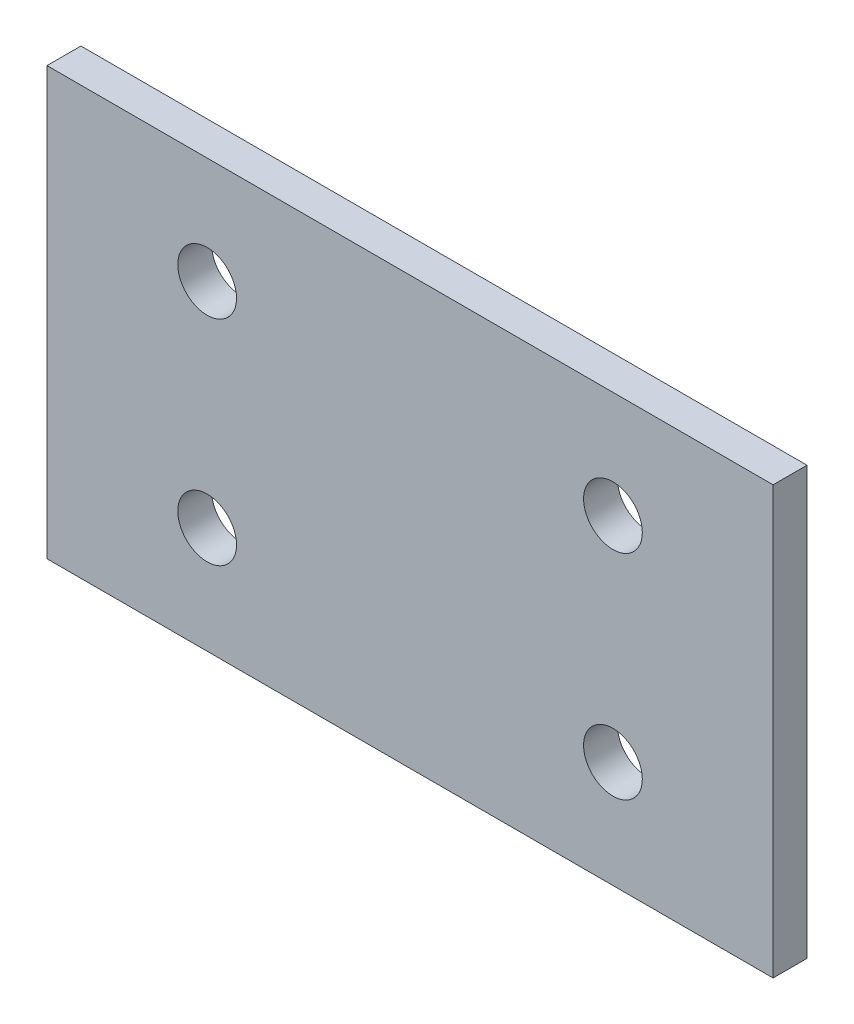
SolidWorks part; units mm, degrees
ref_plane "Front Plane" through (0, 0, 0) normal (0, 0, 1) x (1, 0, 0)
ref_plane "Top Plane" through (0, 0, 0) normal (0, 1, 0) x (1, 0, 0)
ref_plane "Right Plane" through (0, 0, 0) normal (1, 0, 0) x (0, 0, -1)
sketch "Sketch1" plane through (0, 0, 0) normal (0, 0, 1) x (1, 0, 0)
  line L1 (0, 0) -> (68, 0)
  line L2 (0, 0) -> (0, 40)
  line L3 (0, 40) -> (68, 40)
  line L4 (68, 0) -> (68, 40)
  dimension "D1" = 68
  dimension "D2" = 40
extrude "Boss-Extrude1" add sketch "Sketch1" along normal blind 3.175
sketch "Sketch2" plane through (0, 0, 3.175) normal (0, 0, 1) x (1, 0, 0)
  line L0 (68, 40) -> (0, 40) construction
  line L1 (0, 0) -> (68, 0) construction
  line L2 (0, 40) -> (0, 0) construction
  line L3 (68, 0) -> (68, 40) construction
  circle A0 centre (15, 30) radius 2.75
  circle A1 centre (53, 30) radius 2.75
  circle A2 centre (15, 10) radius 2.75
  circle A3 centre (53, 10) radius 2.75
  dimension "D9" = 5.5
  dimension "D10" = 5.5
  dimension "D11" = 5.5
  dimension "D12" = 5.5
  dimension "D1" = 10
  dimension "D2" = 10
  dimension "D3" = 10
  dimension "D4" = 10
  dimension "D5" = 15
  dimension "D6" = 15
  dimension "D7" = 15
  dimension "D8" = 15
extrude "Cut-Extrude1" cut sketch "Sketch2" against normal through all
